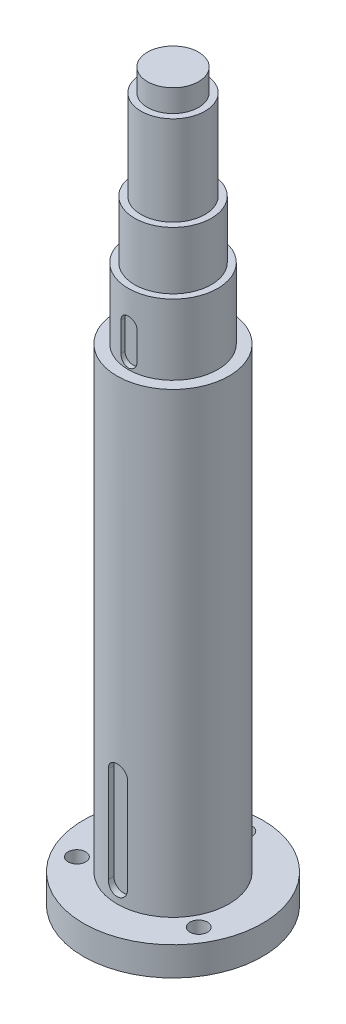
SolidWorks part; units mm, degrees
material "1023 Carbon Steel Sheet (SS)"
ref_plane "Front" through (0, 0, 0) normal (0, 0, 1) x (1, 0, 0)
ref_plane "Top" through (0, 0, 0) normal (0, 1, 0) x (1, 0, 0)
ref_plane "Right" through (0, 0, 0) normal (1, 0, 0) x (0, 0, -1)
sketch "Sketch1" plane through (0, 0, 0) normal (0, 0, 1) x (1, 0, 0)
  line L0 (0, 0) -> (28, 0)
  line L1 (28, 0) -> (28, 9)
  line L2 (28, 9) -> (17.5, 9)
  line L3 (17.5, 9) -> (17.5, 152)
  line L4 (17.5, 152) -> (14, 152)
  line L5 (14, 152) -> (14, 174)
  line L6 (14, 174) -> (12, 174)
  line L7 (12, 174) -> (12, 192)
  line L8 (12, 192) -> (10, 192)
  line L9 (10, 192) -> (10, 220)
  line L10 (10, 220) -> (8, 220)
  line L11 (8, 220) -> (8, 227)
  line L12 (8, 227) -> (0, 227)
  line L13 (0, 340.0777) -> (0, -50.8908) construction
  line L14 (0, 0) -> (0, 227)
  dimension "D1" = 28
  dimension "D2" = 9
  dimension "D3" = 17.5
  dimension "D4" = 14
  dimension "D5" = 12
  dimension "D6" = 10
  dimension "D7" = 8
  dimension "D8" = 7
  dimension "D9" = 28
  dimension "D10" = 18
  dimension "D11" = 22
  dimension "D12" = 143
  dimension "D13" = 8
revolve "Revolve1" add sketch "Sketch1" angle 360 about L13
cosmetic thread "Cosmetic Thread1" parameters "D1"=16, "D2"=21.797
ref_plane "Plane1" through (0, 0, 17.5) normal (0, 0, 1) x (1, 0, 0)
sketch "Sketch2" plane through (0, 0, 17.5) normal (0, 0, 1) x (1, 0, 0)
  line L0 (0, 44) -> (0, 14) construction
  line L1 (3, 44) -> (3, 14)
  line L2 (-3, 44) -> (-3, 14)
  line L3 (17.5, 9) -> (-17.5, 9) construction
  arc A0 (3, 44) -> (-3, 44) centre (0, 44) ccw
  arc A1 (-3, 14) -> (3, 14) centre (0, 14) ccw
  point P3 (0, 29)
  dimension "D1" = 36
  dimension "D3" = 2
  dimension "D2" = 6
extrude "Cut-Extrude1" cut sketch "Sketch2" against normal blind 2
ref_plane "Plane2" through (0, 0, 14) normal (0, 0, 1) x (1, 0, 0)
sketch "Sketch3" plane through (0, 0, 14) normal (0, 0, 1) x (1, 0, 0)
  line L0 (0, 164) -> (0, 155) construction
  line L1 (2.5, 164) -> (2.5, 155)
  line L2 (-2.5, 164) -> (-2.5, 155)
  line L3 (17.5, 152) -> (-17.5, 152) construction
  arc A0 (2.5, 164) -> (-2.5, 164) centre (0, 164) ccw
  arc A1 (-2.5, 155) -> (2.5, 155) centre (0, 155) ccw
  point P3 (0, 159.5)
  dimension "D1" = 0.5
  dimension "D3" = 14
  dimension "D2" = 5
extrude "Cut-Extrude2" cut sketch "Sketch3" against normal blind 1.5
sketch "Sketch7" plane through (0, 0, 0) normal (0, -1, 0) x (1, 0, 0)
  circle A0 centre (0, -22) radius 2.75
  dimension "D1" = 5.5
  dimension "D2" = 22
extrude "Cut-Extrude3" cut sketch "Sketch7" against normal up to next (9 mm away)
sketch "Sketch8" plane through (0, 0, 0) normal (0, -1, 0) x (1, 0, 0)
  circle A0 centre (0, -22) radius 4.5
  dimension "D1" = 9
extrude "Cut-Extrude4" cut sketch "Sketch8" against normal blind 5
pattern_circular "CirPattern1" count 3 every 120 about axis through (0, 0, 0) along (0, 1, 0) of "Cut-Extrude3"
pattern_circular "CirPattern2" count 3 every 120 about axis through (0, 0, 0) along (0, 1, 0) of "Cut-Extrude4"
